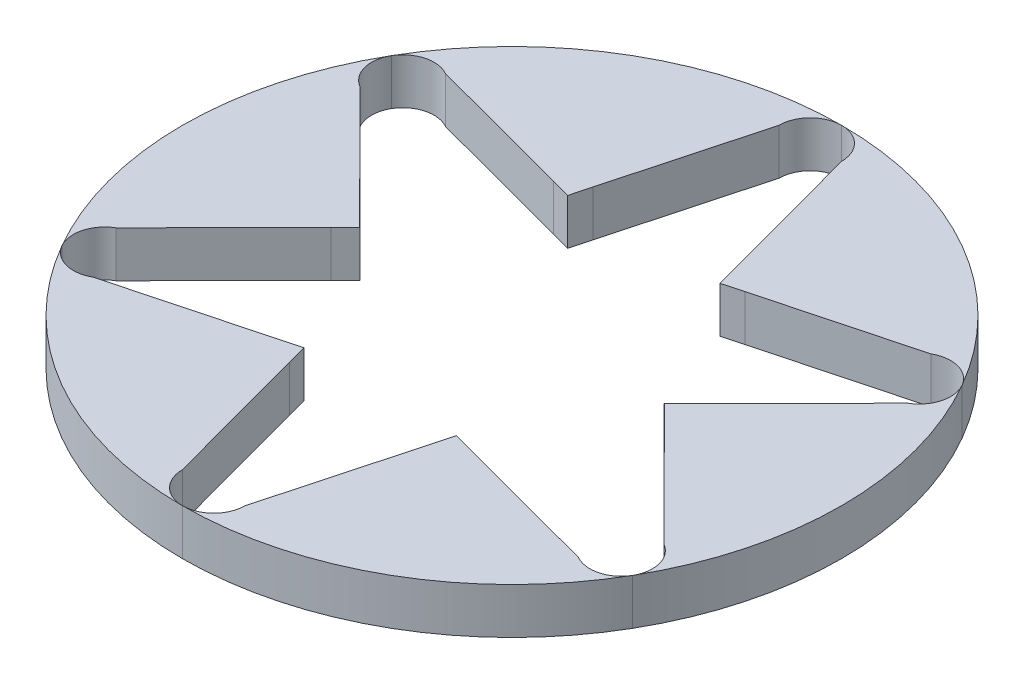
SolidWorks part; units mm, degrees
ref_plane "前基準面" through (0, 0, 0) normal (0, 0, 1) x (1, 0, 0)
ref_plane "上基準面" through (0, 0, 0) normal (0, 1, 0) x (1, 0, 0)
ref_plane "右基準面" through (0, 0, 0) normal (1, 0, 0) x (0, 0, -1)
sketch "草圖1" plane through (0, 0, 0) normal (0, 1, 0) x (1, 0, 0)
  circle A0 centre (0, 0) radius 15.8
  dimension "D1" = 31.6
extrude "填料-伸長1" add sketch "草圖1" along normal blind 2.2
sketch "草圖3" plane through (0, 0, 0) normal (0, -1, 0) x (1, 0, 0)
  line L0 (0, 15.8) -> (0, 15.7286) construction
  line L5 (0, 15.8) -> (0, 15.7286) construction
  line L9 (-1.5, 14.3) -> (-3.4, 7.2726)
  line L10 (-3.4, 7.2726) -> (-3.6501, 6.3221)
  line L13 (1.5, 14.3) -> (3.4, 7.2726)
  line L14 (3.4, 7.2726) -> (3.6501, 6.3221)
  line L15 (11.6342, 8.449) -> (4.5982, 6.5808)
  line L16 (13.1342, 5.851) -> (7.9982, 0.6918)
  line L17 (4.5982, 6.5808) -> (3.6501, 6.3221)
  line L18 (7.9982, 0.6918) -> (7.3001, 0)
  line L19 (13.1342, -5.851) -> (7.9982, -0.6918)
  line L20 (11.6342, -8.449) -> (4.5982, -6.5808)
  line L21 (7.9982, -0.6918) -> (7.3001, 0)
  line L22 (4.5982, -6.5808) -> (3.6501, -6.3221)
  line L23 (1.5, -14.3) -> (3.4, -7.2726)
  line L24 (-1.5, -14.3) -> (-3.4, -7.2726)
  line L25 (3.4, -7.2726) -> (3.6501, -6.3221)
  line L26 (-3.4, -7.2726) -> (-3.6501, -6.3221)
  line L27 (-11.6342, -8.449) -> (-4.5982, -6.5808)
  line L28 (-13.1342, -5.851) -> (-7.9982, -0.6918)
  line L29 (-4.5982, -6.5808) -> (-3.6501, -6.3221)
  line L30 (-7.9982, -0.6918) -> (-7.3001, 0)
  line L31 (-13.1342, 5.851) -> (-7.9982, 0.6918)
  line L32 (-11.6342, 8.449) -> (-4.5982, 6.5808)
  line L33 (-7.9982, 0.6918) -> (-7.3001, 0)
  line L34 (-4.5982, 6.5808) -> (-3.6501, 6.3221)
  circle A1 centre (0, 0) radius 15.8 construction
  arc A2 (0, 15.8) -> (-1.5, 14.3) centre (0, 14.3) ccw
  arc A3 (0, 15.8) -> (1.5, 14.3) centre (0, 14.3) cw
  arc A4 (13.6832, 7.9) -> (11.6342, 8.449) centre (12.3842, 7.15) ccw
  arc A5 (13.6832, 7.9) -> (13.1342, 5.851) centre (12.3842, 7.15) cw
  arc A6 (13.6832, -7.9) -> (13.1342, -5.851) centre (12.3842, -7.15) ccw
  arc A7 (13.6832, -7.9) -> (11.6342, -8.449) centre (12.3842, -7.15) cw
  arc A8 (0, -15.8) -> (1.5, -14.3) centre (0, -14.3) ccw
  arc A9 (0, -15.8) -> (-1.5, -14.3) centre (0, -14.3) cw
  arc A10 (-13.6832, -7.9) -> (-11.6342, -8.449) centre (-12.3842, -7.15) ccw
  arc A11 (-13.6832, -7.9) -> (-13.1342, -5.851) centre (-12.3842, -7.15) cw
  arc A12 (-13.6832, 7.9) -> (-13.1342, 5.851) centre (-12.3842, 7.15) ccw
  arc A13 (-13.6832, 7.9) -> (-11.6342, 8.449) centre (-12.3842, 7.15) cw
  point P12 (0, 14.3)
  point P69 (0, 0)
  dimension "D2" = 1.5
  dimension "D5" = 1.5
  dimension "D6" = 6
extrude "除料-伸長2" cut sketch "草圖3" against normal blind 2.2
